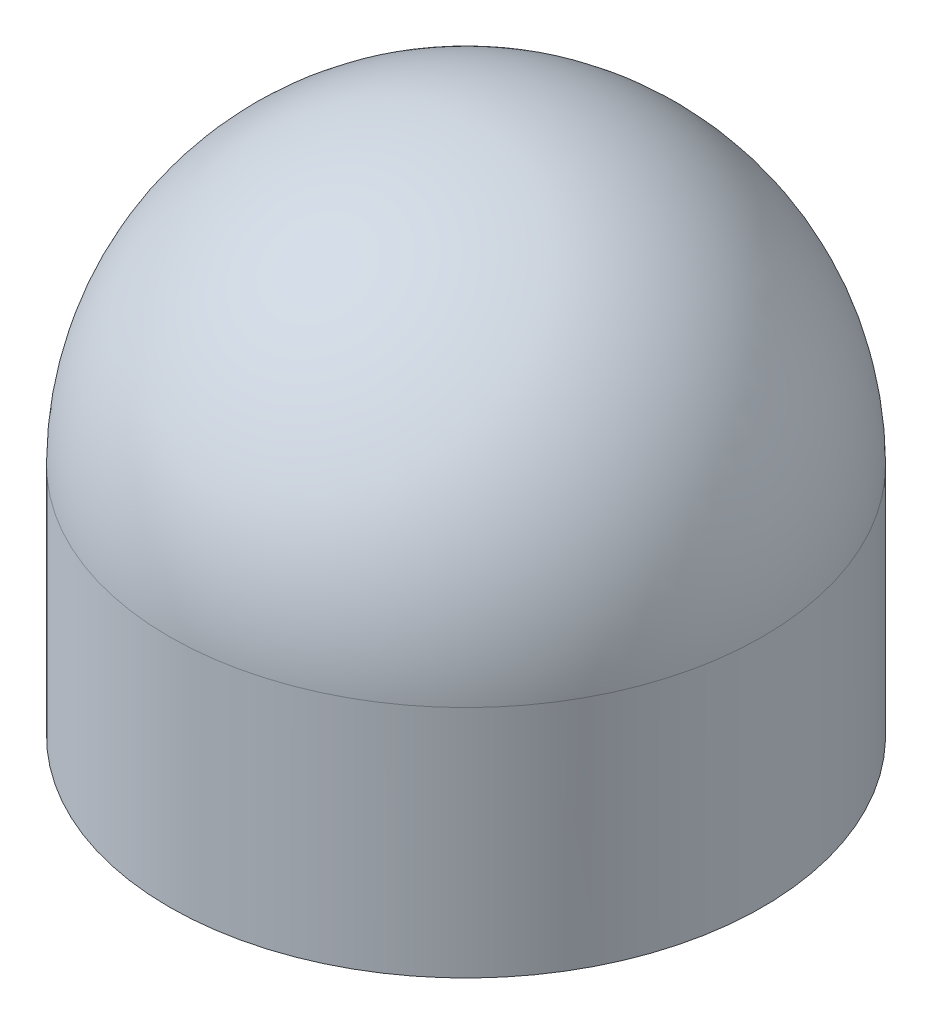
SolidWorks part; units mm, degrees
ref_plane "Ön Düzlem" through (0, 0, 0) normal (0, 0, 1) x (1, 0, 0)
ref_plane "Üst Düzlem" through (0, 0, 0) normal (0, 1, 0) x (1, 0, 0)
ref_plane "Sağ Düzlem" through (0, 0, 0) normal (1, 0, 0) x (0, 0, -1)
sketch "Çizim1" plane through (0, 0, 0) normal (0, 0, 1) x (1, 0, 0)
  line L0 (0, 17.272) -> (0, 7.62)
  line L1 (0, 0) -> (9.652, 0)
  line L2 (0, 0) -> (0, 7.62)
  line L4 (9.652, 0) -> (9.652, 7.62)
  arc A0 (9.652, 7.62) -> (0, 17.272) centre (0, 7.62) ccw
  dimension "D3" = 9.652
  dimension "D1" = 9.652
  dimension "D2" = 7.62
revolve "Döndür1" add sketch "Çizim1" angle 360 about L0
